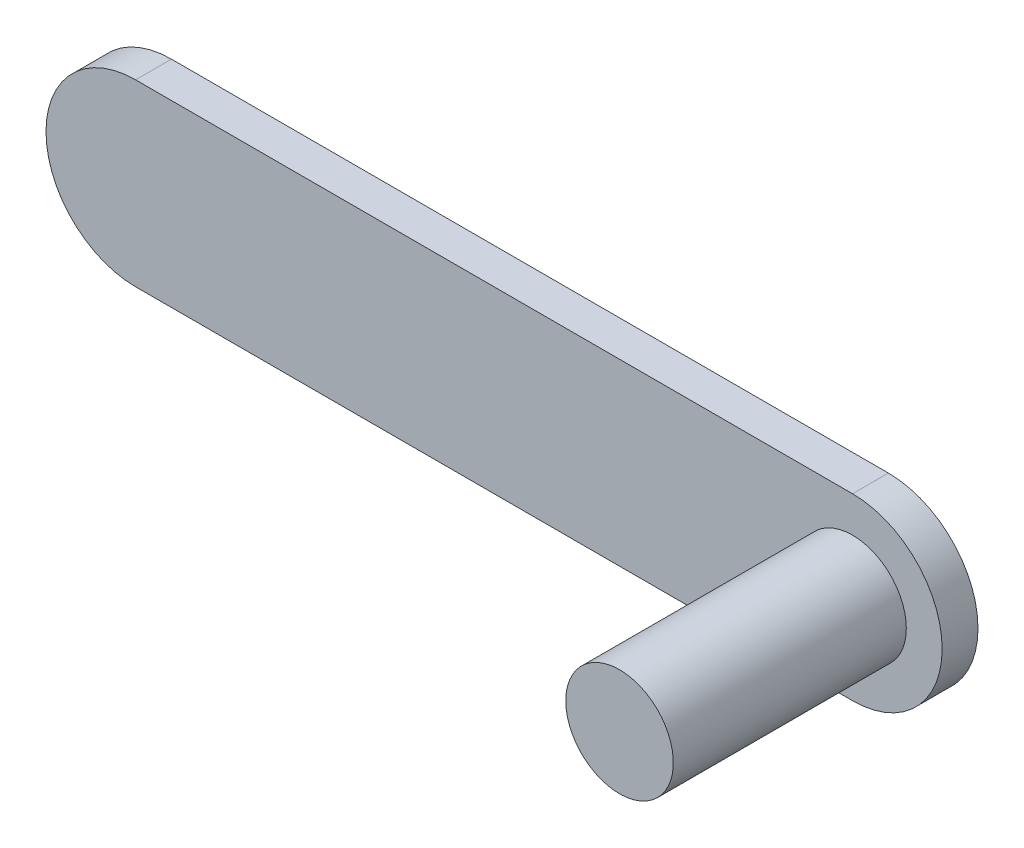
SolidWorks part; units mm, degrees
ref_plane "前视基准面" through (0, 0, 0) normal (0, 0, 1) x (1, 0, 0)
ref_plane "上视基准面" through (0, 0, 0) normal (0, 1, 0) x (1, 0, 0)
ref_plane "右视基准面" through (0, 0, 0) normal (1, 0, 0) x (0, 0, -1)
sketch "草图1" plane through (0, 0, 0) normal (0, 0, 1) x (1, 0, 0)
  line L0 (-65, 5) -> (15, 5) construction
  line L1 (-25, 5) -> (15, 5)
  line L3 (-25, -5) -> (15, -5)
  arc A0 (15, -5) -> (15, 5) centre (15, 0) ccw
  arc A1 (-25, 5) -> (-25, -5) centre (-25, 0) ccw
extrude "凸台-拉伸1" add sketch "草图1" along normal blind 2
sketch "草图2" plane through (0, 0, 0) normal (0, 0, -1) x (-1, 0, 0)
  circle A1 centre (25, 0) radius 2
extrude "凸台-拉伸2" add sketch "草图2" along normal blind 2
sketch "草图3" plane through (0, 0, 0) normal (0, 0, -1) x (-1, 0, 0)
  circle A0 centre (-15, 0) radius 3
extrude "凸台-拉伸4" add sketch "草图3" against normal blind 15
